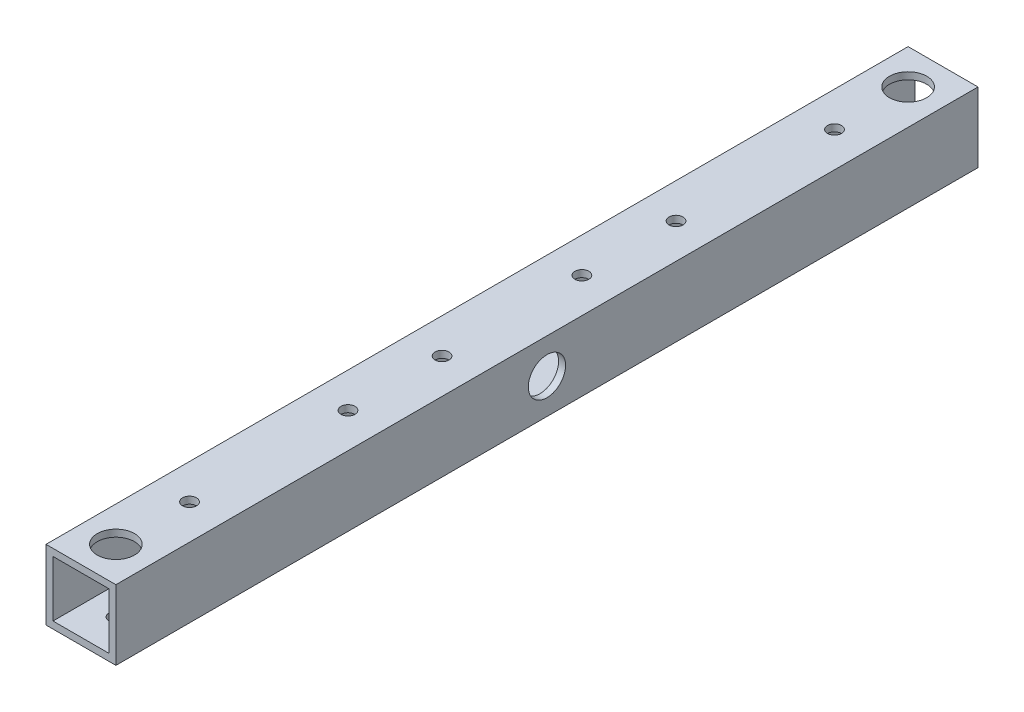
SolidWorks part; units mm, degrees
material "1060 合金"
ref_plane "正面" through (0, 0, 0) normal (0, 0, 1) x (1, 0, 0)
ref_plane "平面" through (0, 0, 0) normal (0, 1, 0) x (1, 0, 0)
ref_plane "右側面" through (0, 0, 0) normal (1, 0, 0) x (0, 0, -1)
sketch "ｽｹｯﾁ1" plane through (0, 0, 0) normal (0, 0, 1) x (1, 0, 0)
  line L1 (-7.0101, 7.7326) -> (7.9899, 7.7326)
  line L2 (-7.0101, 7.7326) -> (-7.0101, -7.2674)
  line L3 (-7.0101, -7.2674) -> (7.9899, -7.2674)
  line L4 (7.9899, 7.7326) -> (7.9899, -7.2674)
  line L9 (-5.5101, 6.2326) -> (6.4899, 6.2326)
  line L10 (-5.5101, 6.2326) -> (-5.5101, -5.7674)
  line L11 (-5.5101, -5.7674) -> (6.4899, -5.7674)
  line L12 (6.4899, 6.2326) -> (6.4899, -5.7674)
  dimension "D1" = 15
  dimension "D2" = 15
  dimension "D3" = 1.5
  dimension "D4" = 1.5
  dimension "D5" = 12
  dimension "D6" = 12
extrude "ﾎﾞｽ - 押し出し2" add sketch "ｽｹｯﾁ1" along normal blind 185
sketch "ｽｹｯﾁ2" plane through (0, 7.7326, 0) normal (0, 1, 0) x (1, 0, 0)
  line L0 (7.9899, -185) -> (-7.0101, -185) construction
  line L1 (-7.0101, -185) -> (-7.0101, 0) construction
  circle A0 centre (0.4899, -177.5) radius 4
  dimension "D1" = 7.5
  dimension "D2" = 7.5
extrude "ｶｯﾄ - 押し出し1" cut sketch "ｽｹｯﾁ2" against normal blind 10
sketch "ｽｹｯﾁ3" plane through (0, -7.2674, 0) normal (0, -1, 0) x (1, 0, 0)
  line L0 (-7.0101, 185) -> (7.9899, 185) construction
  line L1 (7.9899, 185) -> (7.9899, 0) construction
  circle A0 centre (0.4899, 177.5) radius 1.5
  dimension "D1" = 7.5
  dimension "D2" = 7.5
extrude "ｶｯﾄ - 押し出し2" cut sketch "ｽｹｯﾁ3" against normal blind 10
sketch "ｽｹｯﾁ4" plane through (0, 7.7326, 0) normal (0, 1, 0) x (1, 0, 0)
  line L0 (7.9899, 0) -> (-7.0101, 0) construction
  line L1 (7.9899, -185) -> (7.9899, 0) construction
  circle A0 centre (0.4899, -7.5) radius 4
  dimension "D1" = 7.5
  dimension "D2" = 7.5
extrude "ｶｯﾄ - 押し出し3" cut sketch "ｽｹｯﾁ4" against normal blind 10
sketch "ｽｹｯﾁ5" plane through (0, -7.2674, 0) normal (0, -1, 0) x (1, 0, 0)
  line L0 (-7.0101, 0) -> (7.9899, 0) construction
  line L1 (7.9899, 185) -> (7.9899, 0) construction
  circle A0 centre (0.4899, 7.5) radius 1.5
  dimension "D1" = 7.5
  dimension "D2" = 7.5
extrude "ｶｯﾄ - 押し出し4" cut sketch "ｽｹｯﾁ5" against normal blind 10
sketch "ｽｹｯﾁ6" plane through (-7.0101, 0, 0) normal (-1, 0, 0) x (0, 0, 1)
  line L2 (185, -7.2674) -> (0, -7.2674) construction
  circle A0 centre (92.5, 0.2326) radius 1.5
  point P5 (92.5, -7.2674)
extrude "ｶｯﾄ - 押し出し5" cut sketch "ｽｹｯﾁ6" against normal blind 10
sketch "ｽｹｯﾁ7" plane through (7.9899, 0, 0) normal (1, 0, 0) x (0, 0, -1)
  line L0 (-185, 7.7326) -> (0, 7.7326) construction
  circle A0 centre (-92.5, 0.2326) radius 4
  point P5 (-92.5, 7.7326)
  dimension "D1" = 7.5
extrude "ｶｯﾄ - 押し出し6" cut sketch "ｽｹｯﾁ7" against normal blind 10
sketch "ｽｹｯﾁ8" plane through (0, 7.7326, 0) normal (0, 1, 0) x (1, 0, 0)
  line L0 (-7.0101, -92.5) -> (-7.0101, -77.5)
  line L1 (-7.0101, -185) -> (-7.0101, 0) construction
  circle A0 centre (0.4899, -77.5) radius 1.5
  dimension "D2" = 7.5
  dimension "D1" = 15
extrude "ｶｯﾄ - 押し出し7" cut sketch "ｽｹｯﾁ8" against normal blind 10 contours A0
sketch "ｽｹｯﾁ9" plane through (0, 7.7326, 0) normal (0, 1, 0) x (1, 0, 0)
  circle A0 centre (0.4899, -107.5) radius 1.5
  circle A1 centre (0.4899, -77.5) radius 1.5 construction
  dimension "D1" = 30
extrude "ｶｯﾄ - 押し出し8" cut sketch "ｽｹｯﾁ9" against normal blind 10
sketch "ｽｹｯﾁ10" plane through (0, -7.2674, 0) normal (0, -1, 0) x (1, 0, 0)
  line L0 (7.9899, 92.5) -> (7.9899, 77.5)
  line L1 (7.9899, 185) -> (7.9899, 0) construction
  circle A0 centre (0.4899, 77.5) radius 4
  dimension "D2" = 7.5
  dimension "D1" = 15
extrude "ｶｯﾄ - 押し出し9" cut sketch "ｽｹｯﾁ10" against normal blind 10 contours A0
sketch "ｽｹｯﾁ11" plane through (0, -7.2674, 0) normal (0, -1, 0) x (1, 0, 0)
  circle A0 centre (0.4899, 107.5) radius 4
  circle A1 centre (0.4899, 77.5) radius 4 construction
  dimension "D1" = 30
extrude "ｶｯﾄ - 押し出し10" cut sketch "ｽｹｯﾁ11" against normal blind 10
sketch "ｽｹｯﾁ12" plane through (0, 7.7326, 0) normal (0, 1, 0) x (1, 0, 0)
  line L0 (7.9899, 0) -> (-7.0101, 0) construction
  circle A0 centre (0.4899, -23.3) radius 1.5
  dimension "D1" = 23.3
extrude "ｶｯﾄ - 押し出し11" cut sketch "ｽｹｯﾁ12" against normal blind 10
sketch "ｽｹｯﾁ14" plane through (0, 7.7326, 0) normal (0, 1, 0) x (1, 0, 0)
  circle A0 centre (0.4899, -57.3) radius 1.5
  circle A1 centre (0.4899, -23.3) radius 1.5 construction
  dimension "D1" = 34
extrude "ｶｯﾄ - 押し出し12" cut sketch "ｽｹｯﾁ14" against normal blind 10
sketch "ｽｹｯﾁ15" plane through (0, -7.2674, 0) normal (0, -1, 0) x (1, 0, 0)
  circle A0 centre (0.4899, 23.3) radius 4
  circle A1 centre (0.4899, 23.3) radius 1.5 construction
extrude "ｶｯﾄ - 押し出し13" cut sketch "ｽｹｯﾁ15" against normal blind 10
sketch "ｽｹｯﾁ16" plane through (0, -7.2674, 0) normal (0, -1, 0) x (1, 0, 0)
  circle A0 centre (0.4899, 57.3) radius 4
  circle A1 centre (0.4899, 57.3) radius 1.5 construction
extrude "ｶｯﾄ - 押し出し14" cut sketch "ｽｹｯﾁ16" against normal blind 10
sketch "ｽｹｯﾁ18" plane through (0, 7.7326, 0) normal (0, 1, 0) x (1, 0, 0)
  line L0 (7.9899, -185) -> (-7.0101, -185) construction
  line L1 (7.9899, -185) -> (7.9899, 0) construction
  circle A0 centre (0.4899, -161.7) radius 1.5
  dimension "D1" = 23.3
  dimension "D2" = 7.5
extrude "ｶｯﾄ - 押し出し15" cut sketch "ｽｹｯﾁ18" against normal blind 10
sketch "ｽｹｯﾁ19" plane through (0, 7.7326, 0) normal (0, 1, 0) x (1, 0, 0)
  line L0 (7.9899, -185) -> (7.9899, 0) construction
  circle A0 centre (0.4899, -127.7) radius 1.5
  circle A1 centre (0.4899, -161.7) radius 1.5 construction
  dimension "D1" = 34
  dimension "D2" = 7.5
extrude "ｶｯﾄ - 押し出し16" cut sketch "ｽｹｯﾁ19" against normal blind 10
sketch "ｽｹｯﾁ20" plane through (0, -7.2674, 0) normal (0, -1, 0) x (1, 0, 0)
  circle A0 centre (0.4899, 161.7) radius 4
  circle A1 centre (0.4899, 161.7) radius 1.5 construction
extrude "ｶｯﾄ - 押し出し17" cut sketch "ｽｹｯﾁ20" against normal blind 10
sketch "ｽｹｯﾁ21" plane through (0, -7.2674, 0) normal (0, -1, 0) x (-1, 0, 0)
  circle A1 centre (-0.4899, -127.7) radius 4
  circle A2 centre (-0.4899, -127.7) radius 1.5 construction
extrude "ｶｯﾄ - 押し出し18" cut sketch "ｽｹｯﾁ21" against normal blind 10
